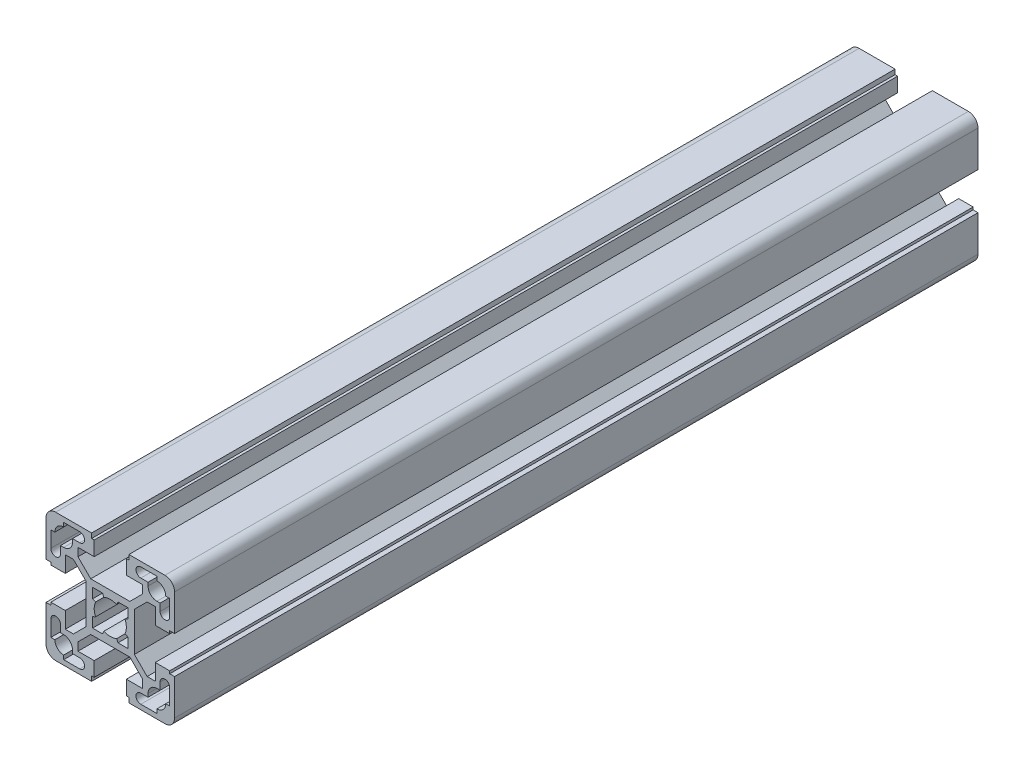
SolidWorks part; units mm, degrees
material "6061 Alloy"
ref_plane "Front Plane" through (0, 0, 0) normal (0, 0, 1) x (1, 0, 0)
ref_plane "Top Plane" through (0, 0, 0) normal (0, 1, 0) x (1, 0, 0)
ref_plane "Right Plane" through (0, 0, 0) normal (1, 0, 0) x (0, 0, -1)
sketch "Sketch1" plane through (0, 0, 0) normal (0, 0, 1) x (1, 0, 0)
  line L0 (5.8, -20) -> (17, -20)
  line L1 (14, -10.05) -> (11.4642, -10.05)
  line L2 (0, -21.1722) -> (0, 18.817) construction
  line L3 (0, 21.1722) -> (0, -18.817) construction
  line L4 (14.5, -18.5) -> (9.5, -18.5)
  line L5 (18.5, 5) -> (14, 5)
  line L6 (6.0858, -7.5) -> (10.05, -11.4642)
  line L7 (20, 5.8) -> (18.5, 5.8)
  line L8 (14, 5) -> (14, 10.05)
  line L9 (18.5, 5.8) -> (18.5, 5)
  line L10 (18.5, 14.5) -> (17.25, 14.5)
  line L11 (14.5, 11.75) -> (15.5, 11.75)
  line L12 (14.5, 17.25) -> (14.5, 18.5)
  line L13 (18.5, 9.5) -> (18.5, 14.5)
  line L14 (15.5, 11.75) -> (15.5, 9.5)
  line L15 (20, 17) -> (20, 5.8)
  line L16 (5.5, 5.5) -> (2.3979, 5.5)
  line L17 (2.3979, 5.5) -> (1.9983, 4.5833)
  line L18 (5.5, 2.3979) -> (5.5, 5.5)
  line L19 (4.5833, 1.9983) -> (5.5, 2.3979)
  line L20 (5, -14) -> (5, -18.5)
  line L21 (11.4642, 10.05) -> (7.5, 6.0858)
  line L22 (-6.0858, 7.5) -> (6.0858, 7.5)
  line L23 (11.75, 15.5) -> (11.75, 14.5)
  line L24 (5, -18.5) -> (5.8, -18.5)
  line L25 (5.8, -18.5) -> (5.8, -20)
  line L26 (10.05, -11.4642) -> (10.05, -14)
  line L27 (10.05, -14) -> (5, -14)
  line L28 (9.5, -15.5) -> (11.75, -15.5)
  line L29 (11.75, -15.5) -> (11.75, -14.5)
  line L30 (9.5, 15.5) -> (11.75, 15.5)
  line L31 (10.05, 14) -> (5, 14)
  line L32 (10.05, 11.4642) -> (10.05, 14)
  line L33 (5.8, 18.5) -> (5.8, 20)
  line L34 (5, 18.5) -> (5.8, 18.5)
  line L35 (7.5, -6.0858) -> (7.5, 6.0858)
  line L36 (5, 14) -> (5, 18.5)
  line L37 (6.0858, 7.5) -> (10.05, 11.4642)
  line L38 (14.5, 18.5) -> (9.5, 18.5)
  line L39 (14, 10.05) -> (11.4642, 10.05)
  line L40 (5.8, 20) -> (17, 20)
  line L41 (-18.5, -5) -> (-14, -5)
  line L42 (-6.0858, -7.5) -> (6.0858, -7.5)
  line L43 (11.4642, -10.05) -> (7.5, -6.0858)
  line L44 (-20, -5.8) -> (-18.5, -5.8)
  line L45 (-14, -5) -> (-14, -10.05)
  line L46 (-18.5, -5.8) -> (-18.5, -5)
  line L47 (-18.5, -14.5) -> (-17.25, -14.5)
  line L48 (4.5833, -1.9983) -> (5.5, -2.3979)
  line L49 (5.5, -2.3979) -> (5.5, -5.5)
  line L50 (2.3979, -5.5) -> (1.9983, -4.5833)
  line L51 (5.5, -5.5) -> (2.3979, -5.5)
  line L52 (-14.5, -11.75) -> (-15.5, -11.75)
  line L53 (-14.5, -17.25) -> (-14.5, -18.5)
  line L54 (-18.5, -9.5) -> (-18.5, -14.5)
  line L55 (-15.5, -11.75) -> (-15.5, -9.5)
  line L56 (-20, -17) -> (-20, -5.8)
  line L57 (-5.5, -5.5) -> (-2.3979, -5.5)
  line L58 (-2.3979, -5.5) -> (-1.9983, -4.5833)
  line L59 (-5.5, -2.3979) -> (-5.5, -5.5)
  line L60 (-4.5833, -1.9983) -> (-5.5, -2.3979)
  line L61 (-11.4642, -10.05) -> (-7.5, -6.0858)
  line L62 (-5.8, 20) -> (-17, 20)
  line L63 (-14, 10.05) -> (-11.4642, 10.05)
  line L64 (-14.5, 18.5) -> (-9.5, 18.5)
  line L65 (-6.0858, 7.5) -> (-10.05, 11.4642)
  line L66 (-5, 14) -> (-5, 18.5)
  line L67 (-7.5, -6.0858) -> (-7.5, 6.0858)
  line L68 (-5, 18.5) -> (-5.8, 18.5)
  line L69 (-5.8, 18.5) -> (-5.8, 20)
  line L70 (-10.05, 11.4642) -> (-10.05, 14)
  line L71 (-10.05, 14) -> (-5, 14)
  line L72 (-9.5, 15.5) -> (-11.75, 15.5)
  line L73 (-11.75, -15.5) -> (-11.75, -14.5)
  line L74 (-9.5, -15.5) -> (-11.75, -15.5)
  line L75 (-10.05, -14) -> (-5, -14)
  line L76 (-10.05, -11.4642) -> (-10.05, -14)
  line L77 (-5.8, -18.5) -> (-5.8, -20)
  line L78 (-5, -18.5) -> (-5.8, -18.5)
  line L79 (-11.75, 15.5) -> (-11.75, 14.5)
  line L80 (-11.4642, 10.05) -> (-7.5, 6.0858)
  line L81 (-5, -14) -> (-5, -18.5)
  line L82 (-4.5833, 1.9983) -> (-5.5, 2.3979)
  line L83 (-5.5, 2.3979) -> (-5.5, 5.5)
  line L84 (-2.3979, 5.5) -> (-1.9983, 4.5833)
  line L85 (-5.5, 5.5) -> (-2.3979, 5.5)
  line L86 (-20, 17) -> (-20, 5.8)
  line L87 (-15.5, 11.75) -> (-15.5, 9.5)
  line L88 (20, -17) -> (20, -5.8)
  line L89 (15.5, -11.75) -> (15.5, -9.5)
  line L90 (18.5, -9.5) -> (18.5, -14.5)
  line L91 (14.5, -17.25) -> (14.5, -18.5)
  line L92 (14.5, -11.75) -> (15.5, -11.75)
  line L93 (18.5, -14.5) -> (17.25, -14.5)
  line L94 (-18.5, 9.5) -> (-18.5, 14.5)
  line L95 (-14.5, 17.25) -> (-14.5, 18.5)
  line L96 (18.5, -5.8) -> (18.5, -5)
  line L97 (14, -5) -> (14, -10.05)
  line L98 (20, -5.8) -> (18.5, -5.8)
  line L99 (18.5, -5) -> (14, -5)
  line L100 (-14.5, 11.75) -> (-15.5, 11.75)
  line L101 (-18.5, 14.5) -> (-17.25, 14.5)
  line L102 (-18.5, 5.8) -> (-18.5, 5)
  line L103 (-14, 5) -> (-14, 10.05)
  line L104 (-20, 5.8) -> (-18.5, 5.8)
  line L105 (-6.0858, -7.5) -> (-10.05, -11.4642)
  line L106 (-18.5, 5) -> (-14, 5)
  line L107 (-14.5, -18.5) -> (-9.5, -18.5)
  line L108 (-20, 0) -> (20.788, 0) construction
  line L109 (-14, -10.05) -> (-11.4642, -10.05)
  line L110 (-5.8, -20) -> (-17, -20)
  arc A0 (14.5, -11.75) -> (11.75, -14.5) centre (14.5, -14.5) ccw
  arc A1 (18.5, 9.5) -> (15.5, 9.5) centre (17, 9.5) cw
  arc A2 (14.5, 17.25) -> (17.25, 14.5) centre (14.5, 14.5) cw
  arc A3 (17, 20) -> (20, 17) centre (17, 17) cw
  arc A4 (-1.9983, 4.5833) -> (1.9983, 4.5833) centre (0, 0) cw
  arc A5 (9.5, 15.5) -> (9.5, 18.5) centre (9.5, 17) cw
  arc A6 (9.5, -15.5) -> (9.5, -18.5) centre (9.5, -17) ccw
  arc A7 (14.5, 11.75) -> (11.75, 14.5) centre (14.5, 14.5) cw
  arc A8 (4.5833, -1.9983) -> (4.5833, 1.9983) centre (0, 0) ccw
  arc A9 (-18.5, -9.5) -> (-15.5, -9.5) centre (-17, -9.5) cw
  arc A10 (-14.5, -17.25) -> (-17.25, -14.5) centre (-14.5, -14.5) cw
  arc A11 (-1.9983, -4.5833) -> (1.9983, -4.5833) centre (0, 0) ccw
  arc A12 (-17, -20) -> (-20, -17) centre (-17, -17) cw
  arc A13 (-4.5833, -1.9983) -> (-4.5833, 1.9983) centre (0, 0) cw
  arc A14 (-14.5, 11.75) -> (-11.75, 14.5) centre (-14.5, 14.5) ccw
  arc A15 (-9.5, -15.5) -> (-9.5, -18.5) centre (-9.5, -17) cw
  arc A16 (-9.5, 15.5) -> (-9.5, 18.5) centre (-9.5, 17) ccw
  arc A17 (-17, 20) -> (-20, 17) centre (-17, 17) ccw
  arc A18 (17, -20) -> (20, -17) centre (17, -17) ccw
  arc A19 (14.5, -17.25) -> (17.25, -14.5) centre (14.5, -14.5) ccw
  arc A20 (18.5, -9.5) -> (15.5, -9.5) centre (17, -9.5) ccw
  arc A21 (-14.5, 17.25) -> (-17.25, 14.5) centre (-14.5, 14.5) ccw
  arc A22 (-18.5, 9.5) -> (-15.5, 9.5) centre (-17, 9.5) ccw
  arc A23 (-14.5, -11.75) -> (-11.75, -14.5) centre (-14.5, -14.5) cw
  point P55 (7.5, 0)
  point P101 (-7.5, 0)
  point P116 (0, -7.5)
  point P149 (0, 7.5)
extrude "Extrude1" add sketch "Sketch1" along normal mid plane 250
hole_wizard "M12 Tapped Hole1" positions "3DSketch2" profile "Sketch3" tap size "M12" standard "ISO"
sketch3d "3DSketch2"
  line L0 (-20, 17, 0) -> (-20, 5.8, 0) construction
  line L1 (-5.8, 20, 0) -> (-17, 20, 0) construction
  line L2 (-5.8, 20, 200) -> (-17, 20, 200) construction
  line L3 (-20, 17, 200) -> (-20, 5.8, 200) construction
  point P0 (0, 0, 200)
  point P2 (0, 0, 0)
  dimension "D1" = 20
  dimension "D2" = 20
  dimension "D3" = 20
  dimension "D4" = 20
sketch "Sketch3" plane through (0, 0, 200) normal (1, 0, 0) x (0, -1, 0)
  line L0 (0, 0) -> (0, 35.8144)
  line L1 (0, 35.8144) -> (5.1, 32.75)
  line L2 (5.1, 32.75) -> (5.1, 0.925)
  line L3 (5.1, 0.925) -> (6.025, 0)
  line L5 (6.025, 0) -> (0, 0)
  line L6 (-5.1, 0.925) -> (-6.025, 0) construction
  line L10 (0, 35.8144) -> (-5.1, 32.75) construction
  line L11 (0, -6.35) -> (0, 107.95) construction
  dimension "Tap Drill Dia." = 10.2
  dimension "Tap Drill Depth" = 32.75
  dimension "Near C'Sink Dia." = 12.05
  dimension "Near C'Sink Angle" = 90
  dimension "Drill Angle" = 118
cosmetic thread "Hole Thread1" [suppressed] parameters "D1"=24, "D2"=12
cosmetic thread "Hole Thread2" [suppressed] parameters "D1"=24, "D2"=12
hole_wizard "Ø9.8 (9.8) Diameter Hole1" positions "3DSketch3" profile "Sketch4" hole size "Ø9.8" standard "ISO"
sketch3d "3DSketch3"
  line L0 (-5.8, 20, 200) -> (-17, 20, 200) construction
  line L1 (20, -17, 200) -> (20, -5.8, 200) construction
  line L2 (17, 20, 0) -> (5.8, 20, 0) construction
  line L3 (20, -17, 0) -> (20, -5.8, 0) construction
  point P0 (0, 20, 184)
  point P2 (20, 0, 184)
  point P4 (0, 20, 16)
  point P6 (20, 0, 16)
  dimension "D1" = 16
  dimension "D2" = 20
  dimension "D3" = 20
  dimension "D4" = 16
  dimension "D5" = 16
  dimension "D6" = 16
sketch "Sketch4" plane through (0, 20, 184) normal (1, 0, 0) x (0, 0, 1)
  line L0 (0, 0) -> (0, 40)
  line L1 (0, 40) -> (4.9, 40)
  line L2 (4.9, 40) -> (4.9, 0)
  line L5 (4.9, 0) -> (0, 0)
  line L11 (0, -6.35) -> (0, 107.95) construction
  dimension "Thru Hole Dia." = 9.8
  dimension "Thru Hole Depth" = 40
hole_wizard "Ø17.0 (17) Diameter Hole1" positions "3DSketch4" profile "Sketch5" hole size "Ø17.0" standard "ISO"
sketch3d "3DSketch4"
  line L0 (-5.8, 20, 200) -> (-17, 20, 200) construction
  line L1 (-5.8, 20, 0) -> (-17, 20, 0) construction
  point P0 (0, 20, 177.5)
  point P2 (0, 20, 22.5)
  dimension "D1" = 20
  dimension "D2" = 22.5
  dimension "D3" = 22.5
sketch "Sketch5" plane through (0, 20, 177.5) normal (1, 0, 0) x (0, 0, 1)
  line L0 (0, 0) -> (0, 40)
  line L1 (0, 40) -> (8.5, 40)
  line L2 (8.5, 40) -> (8.5, 0)
  line L5 (8.5, 0) -> (0, 0)
  line L11 (0, -6.35) -> (0, 107.95) construction
  dimension "Thru Hole Dia." = 17
  dimension "Thru Hole Depth" = 40
